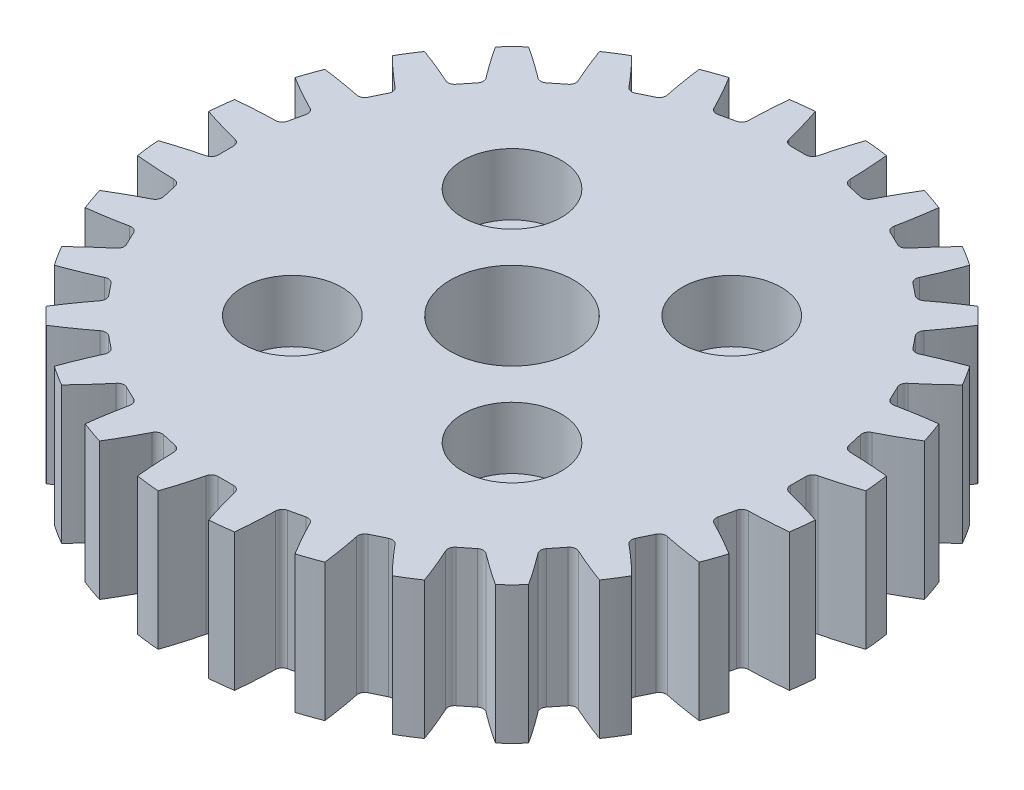
SolidWorks part; units mm, degrees
ref_plane "Front Plane" through (0, 0, 0) normal (0, 0, 1) x (1, 0, 0)
ref_plane "Top Plane" through (0, 0, 0) normal (0, 1, 0) x (1, 0, 0)
ref_plane "Right Plane" through (0, 0, 0) normal (1, 0, 0) x (0, 0, -1)
sketch "Sketch1" plane through (0, 0, 0) normal (0, 1, 0) x (1, 0, 0)
  line L1 (-8, 8) -> (8, 8)
  line L2 (-8, 8) -> (-8, -8)
  line L3 (-8, -8) -> (8, -8)
  line L4 (8, 8) -> (8, -8)
  line L5 (-8, 8) -> (8, -8) construction
  line L6 (-8, -8) -> (8, 8) construction
  circle A0 centre (0, 0) radius 24
  circle A1 centre (0, 0) radius 4.5
  circle A2 centre (-8, 8) radius 2.1
  circle A3 centre (8, 8) radius 2.1
  circle A4 centre (8, -8) radius 2.1
  circle A5 centre (-8, -8) radius 2.1
  dimension "D1" = 48
  dimension "D2" = 9
  dimension "D5" = 4.2
  dimension "D3" = 16
  dimension "D4" = 16
extrude "Boss-Extrude1" add sketch "Sketch1" along normal blind 10 contours A0 A5 L2 A2 L1 A3 L4 A4 L3 | A5 L3 A4 L4 A3 L1 A2 L2 A1
sketch "Sketch2" plane through (0, 10, 0) normal (0, 1, 0) x (1, 0, 0)
  line L0 (0, 17) -> (0, 0) construction
  line L1 (-0.56, 20.84) -> (0.56, 20.84)
  line L2 (0.56, 20.84) -> (0.56, 21.34)
  circle A0 centre (0, 0) radius 20.84
  arc A1 (0.56, 20.84) -> (1.05, 21.2405) centre (0.56, 21.34) ccw
  circle A2 centre (0, 0) radius 24
  arc A4 (1.84, 23.9294) -> (1.05, 21.2405) centre (34.9987, 12.7267) ccw
  arc A5 (-0.56, 20.84) -> (-1.05, 21.2405) centre (-0.56, 21.34) cw
  arc A6 (-1.84, 23.9294) -> (-1.05, 21.2405) centre (-34.9987, 12.7267) cw
  arc A7 (-1.84, 23.9294) -> (1.84, 23.9294) centre (0, 18.1465) cw
  point P17 (0, 20.84)
  dimension "D1" = 41.68
  dimension "D4" = 1.84
  dimension "D5" = 35
  dimension "D7" = 48
  dimension "D2" = 0.56
  dimension "D3" = 0.5
  dimension "D6" = 1.05
extrude "Cut-Extrude1" cut sketch "Sketch2" against normal through all
pattern_circular "CirPattern1" count 28 over 360 about axis through (0, 0, 0) along (0, 1, 0) of "Cut-Extrude1"
sketch "Sketch3" plane through (0, 10, 0) normal (0, 1, 0) x (1, 0, 0)
  circle A0 centre (-8, 8) radius 3.6
  circle A1 centre (8, 8) radius 3.6
  circle A2 centre (8, -8) radius 3.6
  circle A3 centre (-8, -8) radius 3.6
  dimension "D1" = 7.2
extrude "Cut-Extrude2" cut sketch "Sketch3" against normal blind 4.5
